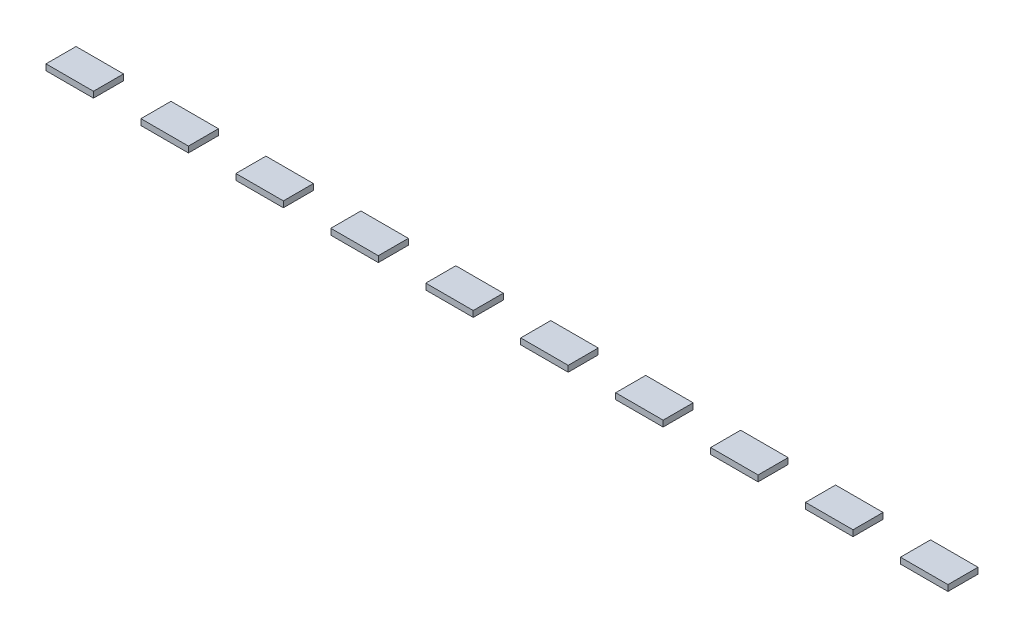
SolidWorks part; units mm, degrees
ref_plane "Front Plane" through (0, 0, 0) normal (0, 0, 1) x (1, 0, 0)
ref_plane "Top Plane" through (0, 0, 0) normal (0, 1, 0) x (1, 0, 0)
ref_plane "Right Plane" through (0, 0, 0) normal (1, 0, 0) x (0, 0, -1)
sketch "Sketch1" plane through (0, 0, 0) normal (0, 1, 0) x (1, 0, 0)
  line L0 (50.165, -6.35) -> (30.099, -6.35)
  line L1 (10.033, -6.35) -> (-10.033, -6.35)
  line L2 (10.033, -6.35) -> (10.033, 6.35)
  line L3 (10.033, 6.35) -> (-10.033, 6.35)
  line L4 (-10.033, -6.35) -> (-10.033, 6.35)
  line L5 (10.033, -6.35) -> (-10.033, 6.35) construction
  line L6 (10.033, 6.35) -> (-10.033, -6.35) construction
  line L7 (50.165, -6.35) -> (50.165, 6.35)
  line L8 (50.165, 6.35) -> (30.099, 6.35)
  line L9 (30.099, -6.35) -> (30.099, 6.35)
  line L10 (50.165, -6.35) -> (30.099, 6.35) construction
  line L11 (50.165, 6.35) -> (30.099, -6.35) construction
  line L12 (90.297, -6.35) -> (70.231, -6.35)
  line L13 (90.297, -6.35) -> (90.297, 6.35)
  line L14 (90.297, 6.35) -> (70.231, 6.35)
  line L15 (70.231, -6.35) -> (70.231, 6.35)
  line L16 (90.297, -6.35) -> (70.231, 6.35) construction
  line L17 (90.297, 6.35) -> (70.231, -6.35) construction
  line L18 (130.429, -6.35) -> (110.363, -6.35)
  line L19 (130.429, -6.35) -> (130.429, 6.35)
  line L20 (130.429, 6.35) -> (110.363, 6.35)
  line L21 (110.363, -6.35) -> (110.363, 6.35)
  line L22 (130.429, -6.35) -> (110.363, 6.35) construction
  line L23 (130.429, 6.35) -> (110.363, -6.35) construction
  line L24 (170.561, -6.35) -> (150.495, -6.35)
  line L25 (170.561, -6.35) -> (170.561, 6.35)
  line L26 (170.561, 6.35) -> (150.495, 6.35)
  line L27 (150.495, -6.35) -> (150.495, 6.35)
  line L28 (170.561, -6.35) -> (150.495, 6.35) construction
  line L29 (170.561, 6.35) -> (150.495, -6.35) construction
  line L30 (210.693, -6.35) -> (190.627, -6.35)
  line L31 (210.693, -6.35) -> (210.693, 6.35)
  line L32 (210.693, 6.35) -> (190.627, 6.35)
  line L33 (190.627, -6.35) -> (190.627, 6.35)
  line L34 (210.693, -6.35) -> (190.627, 6.35) construction
  line L35 (210.693, 6.35) -> (190.627, -6.35) construction
  line L36 (250.825, -6.35) -> (230.759, -6.35)
  line L37 (250.825, -6.35) -> (250.825, 6.35)
  line L38 (250.825, 6.35) -> (230.759, 6.35)
  line L39 (230.759, -6.35) -> (230.759, 6.35)
  line L40 (250.825, -6.35) -> (230.759, 6.35) construction
  line L41 (250.825, 6.35) -> (230.759, -6.35) construction
  line L42 (290.957, -6.35) -> (270.891, -6.35)
  line L43 (290.957, -6.35) -> (290.957, 6.35)
  line L44 (290.957, 6.35) -> (270.891, 6.35)
  line L45 (270.891, -6.35) -> (270.891, 6.35)
  line L46 (290.957, -6.35) -> (270.891, 6.35) construction
  line L47 (290.957, 6.35) -> (270.891, -6.35) construction
  line L48 (331.089, -6.35) -> (311.023, -6.35)
  line L49 (331.089, -6.35) -> (331.089, 6.35)
  line L50 (331.089, 6.35) -> (311.023, 6.35)
  line L51 (311.023, -6.35) -> (311.023, 6.35)
  line L52 (331.089, -6.35) -> (311.023, 6.35) construction
  line L53 (331.089, 6.35) -> (311.023, -6.35) construction
  line L54 (371.221, -6.35) -> (351.155, -6.35)
  line L55 (371.221, -6.35) -> (371.221, 6.35)
  line L56 (371.221, 6.35) -> (351.155, 6.35)
  line L57 (351.155, -6.35) -> (351.155, 6.35)
  line L58 (371.221, -6.35) -> (351.155, 6.35) construction
  line L59 (371.221, 6.35) -> (351.155, -6.35) construction
  point P0 (0, 0)
  point P9 (40.132, 0)
  point P14 (80.264, 0)
  point P19 (120.396, 0)
  point P24 (160.528, 0)
  point P29 (200.66, 0)
  point P34 (240.792, 0)
  point P39 (280.924, 0)
  point P44 (321.056, 0)
  point P49 (361.188, 0)
  dimension "D1" = 10
extrude "Boss-Extrude1" add sketch "Sketch1" along normal blind 2.54
